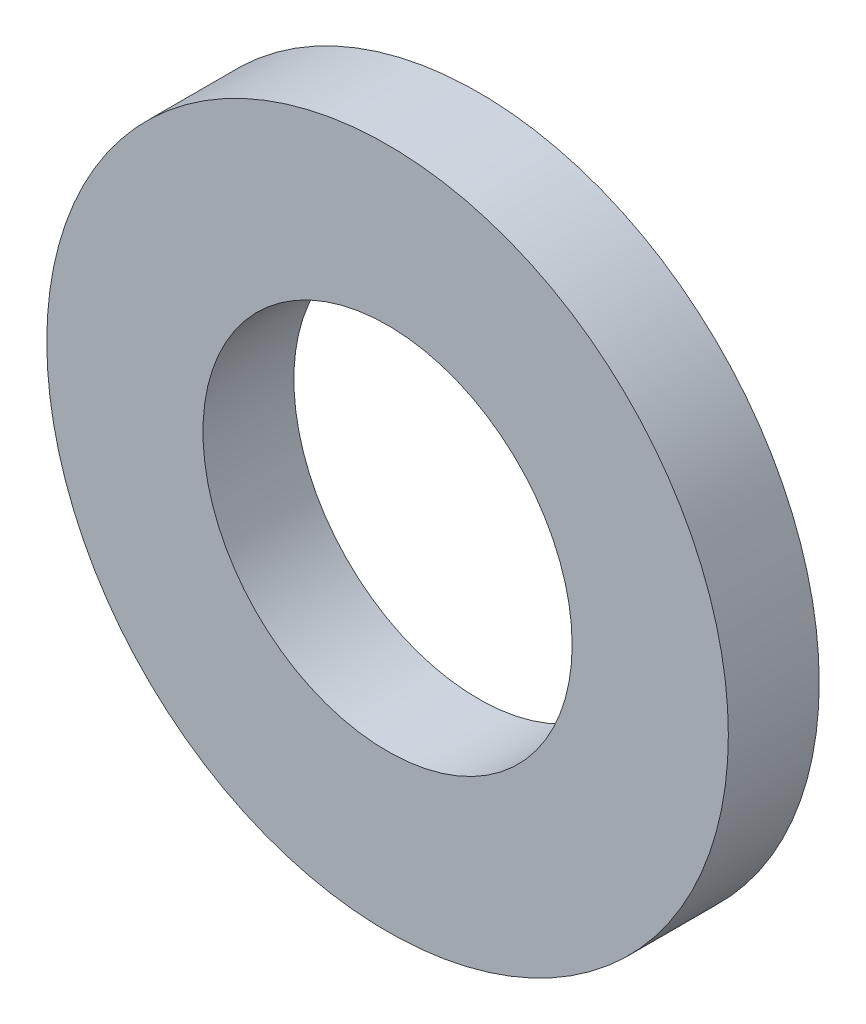
SolidWorks part; units mm, degrees
material "ABS"
ref_plane "Plan de face" through (0, 0, 0) normal (0, 0, 1) x (1, 0, 0)
ref_plane "Plan de dessus" through (0, 0, 0) normal (0, 1, 0) x (1, 0, 0)
ref_plane "Plan de droite" through (0, 0, 0) normal (1, 0, 0) x (0, 0, -1)
sketch "Esquisse1" plane through (0, 0, 0) normal (0, 0, 1) x (1, 0, 0)
  circle A0 centre (0, 0) radius 3.25
  circle A1 centre (0, 0) radius 6
  dimension "D1" = 6.5
  dimension "D2" = 12
extrude "Boss.-Extru.1" add sketch "Esquisse1" along normal mid plane 1.6
